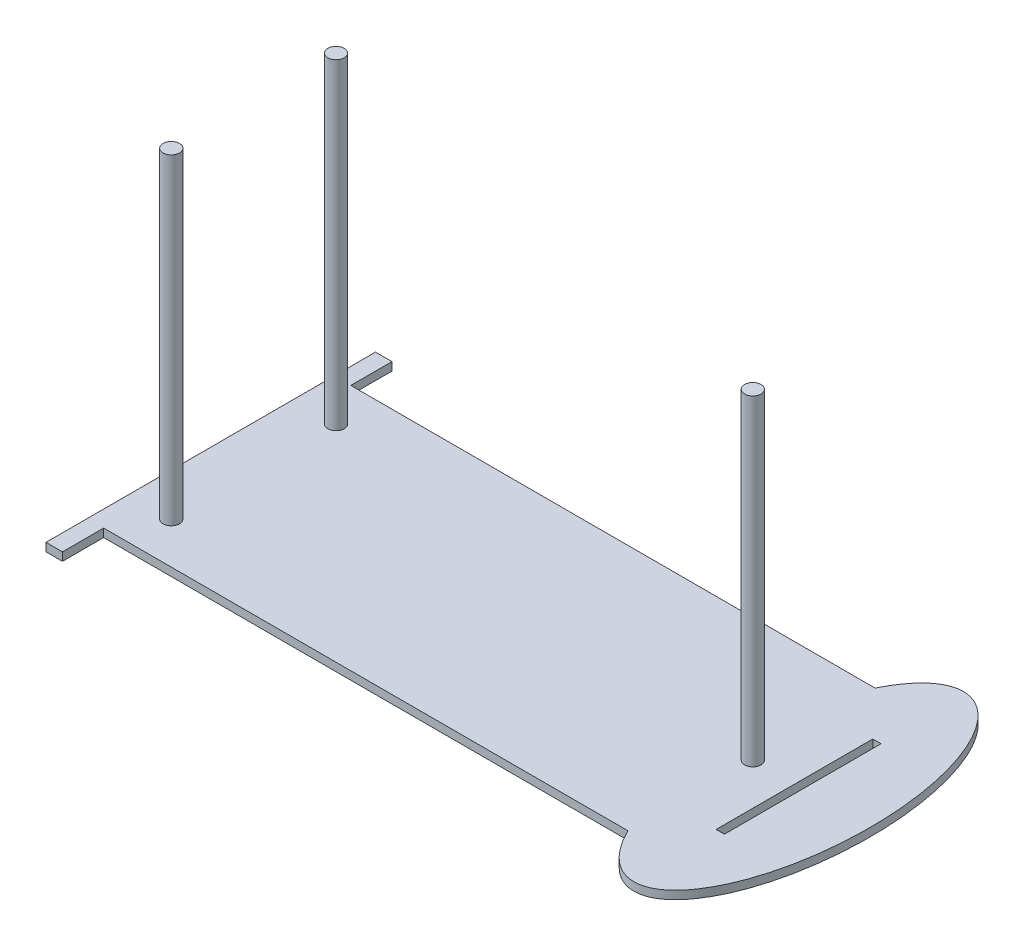
SolidWorks part; units mm, degrees
ref_plane "Front Plane" through (0, 0, 0) normal (0, 0, 1) x (1, 0, 0)
ref_plane "Top Plane" through (0, 0, 0) normal (0, 1, 0) x (1, 0, 0)
ref_plane "Right Plane" through (0, 0, 0) normal (1, 0, 0) x (0, 0, -1)
sketch "Sketch1" plane through (0, 0, 0) normal (0, 1, 0) x (1, 0, 0)
  line L0 (107.2539, 26.1875) -> (108.2558, 26.1875)
  line L1 (-83.4403, 26.1875) -> (78.2122, 26.1875)
  line L2 (-88.5203, 26.1875) -> (-88.5203, -50.0125)
  line L3 (-83.4403, -50.0125) -> (78.2076, -50.0125)
  line L6 (-88.5203, 26.1875) -> (-88.5203, 38.8875)
  line L7 (-88.5203, 38.8875) -> (-83.4403, 38.8875)
  line L8 (-83.4403, 26.1875) -> (-83.4403, 38.8875)
  line L10 (-88.5203, -50.0125) -> (-88.5203, -62.7125)
  line L11 (-88.5203, -62.7125) -> (-83.4403, -62.7125)
  line L12 (-83.4403, -50.0125) -> (-83.4403, -62.7125)
  line L14 (91.4595, -36.0586) -> (93.9995, -36.0586)
  line L15 (91.4595, -36.0586) -> (91.4595, 12.2386)
  line L16 (91.4595, 12.2386) -> (93.9995, 12.2386)
  line L17 (93.9995, -36.0586) -> (93.9995, 12.2386)
  line L18 (91.4595, -36.0586) -> (93.9995, 12.2386) construction
  line L19 (91.4595, 12.2386) -> (93.9995, -36.0586) construction
  ellipse E0 centre (92.7295, -11.91) end of major axis (92.7353, 38.8925) minor radius 21.9502 (78.2076, -50.0125) -> (78.2122, 26.1875) ccw
  dimension "D1" = 2.54
  dimension "D2" = 48.2972
  dimension "D3" = 5.08
  dimension "D4" = 12.7
  dimension "D5" = 5.08
  dimension "D6" = 12.7
extrude "Boss-Extrude1" add sketch "Sketch1" along normal blind 2.54 contours L3 E0 L1 L8 L7 L6 L2 L10 L11 L12
sketch "Sketch2" plane through (0, 2.54, 0) normal (0, 1, 0) x (1, 0, 0)
  line L0 (-83.4403, 26.1875) -> (-75.4035, 26.1875)
  line L1 (-83.4403, 26.1875) -> (78.2122, 26.1875) construction
  circle A0 centre (-75.4035, 13.6003) radius 2.54
  circle A1 centre (-75.4035, -37.2013) radius 2.54
  circle A2 centre (78.6295, -11.9125) radius 2.54
  dimension "D1" = 5.08
  dimension "D2" = 5.08
  dimension "D3" = 5.08
extrude "Boss-Extrude2" add sketch "Sketch2" along normal blind 99.06 contours A0 | A1 | A2
sketch "Sketch6" plane through (0, 0, 0) normal (0, -1, 0) x (-1, 0, 0)
  line L0 (83.4403, -50.0125) -> (2.6164, -50.0125)
  line L1 (83.4403, -50.0125) -> (-78.2076, -50.0125) construction
  line L5 (42.2006, -39.4715) -> (-37.8094, -39.4715)
  line L6 (42.2006, -39.4715) -> (42.2006, 15.6465)
  line L7 (42.2006, 15.6465) -> (-37.8094, 15.6465)
  line L8 (-37.8094, -39.4715) -> (-37.8094, 15.6465)
  point P5 (2.1956, -11.9125)
  dimension "D1" = 55.118
  dimension "D2" = 80.01
extrude "Boss-Extrude3" add sketch "Sketch6" along normal blind 7.62 contours L8 L7 L6 L5
sketch "Sketch7" plane through (0, -7.62, 0) normal (0, -1, 0) x (-1, 0, 0)
  text T0 "Arduino"
